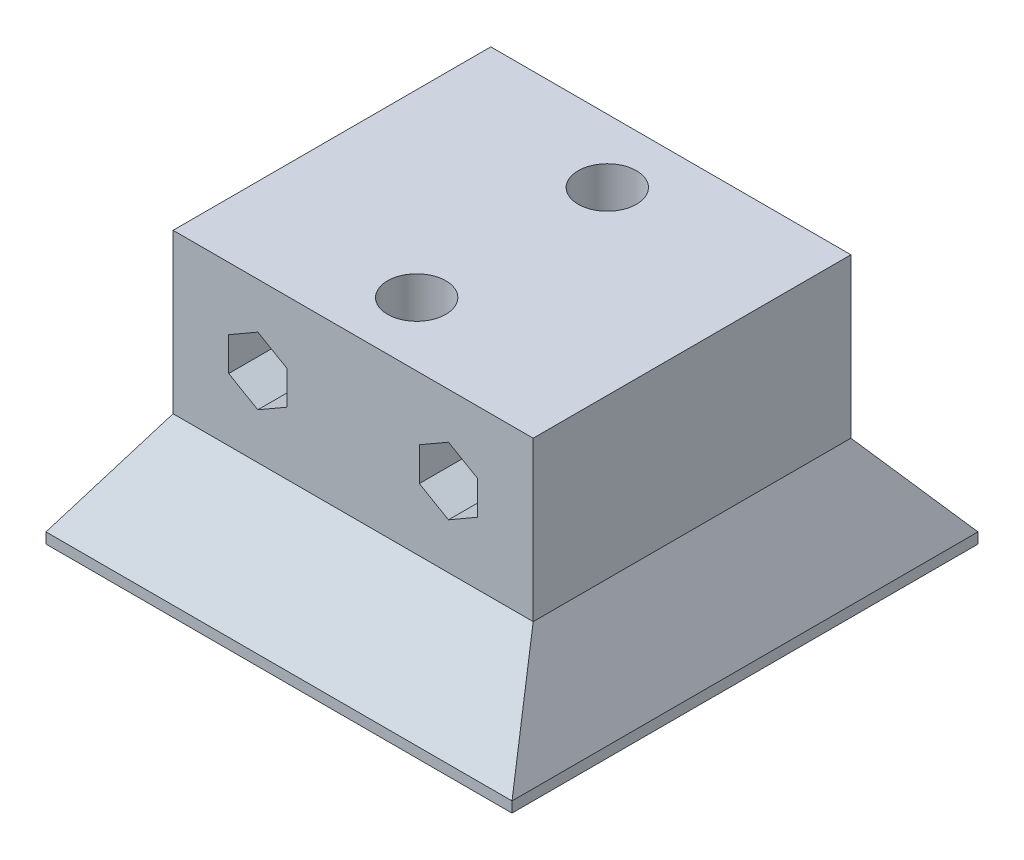
SolidWorks part; units mm, degrees
ref_plane "Front Plane" through (0, 0, 0) normal (0, 0, 1) x (1, 0, 0)
ref_plane "Top Plane" through (0, 0, 0) normal (0, 1, 0) x (1, 0, 0)
ref_plane "Right Plane" through (0, 0, 0) normal (1, 0, 0) x (0, 0, -1)
sketch "Sketch1" plane through (0, 0, 0) normal (0, 0, 1) x (1, 0, 0)
  line L1 (0, 0) -> (34, 0)
  line L2 (0, 0) -> (0, 15)
  line L3 (0, 15) -> (34, 15)
  line L4 (34, 0) -> (34, 15)
  dimension "D1" = 34
  dimension "D2" = 15
extrude "Boss-Extrude1" add sketch "Sketch1" along normal blind 30
sketch "Sketch3" plane through (0, 0, 30) normal (0, 0, 1) x (1, 0, 0)
  line L0 (0, 0) -> (-5, -8.6603)
  line L1 (-5, -9.6603) -> (39, -9.6603)
  line L2 (39, -8.6603) -> (34, 0)
  line L3 (0, 0) -> (34, 0) construction
  line L4 (0, 0) -> (34, 0)
  line L5 (-5, -8.6603) -> (-5, -9.6603)
  line L6 (39, -9.6603) -> (39, -8.6603)
  dimension "D1" = 120
  dimension "D2" = 120
  dimension "D3" = 44
  dimension "D4" = 1
extrude "Boss-Extrude2" add sketch "Sketch3" against normal blind 37 and the other way blind 7
sketch "Sketch5" plane through (0, 0, 30) normal (0, 0, 1) x (1, 0, 0)
  line L0 (34, 15) -> (0, 15) construction
  line L1 (8, 4.3246) -> (10.75, 5.9123)
  line L2 (10.75, 5.9123) -> (10.75, 9.0877)
  line L3 (10.75, 9.0877) -> (8, 10.6754)
  line L4 (8, 10.6754) -> (5.25, 9.0877)
  line L5 (5.25, 9.0877) -> (5.25, 5.9123)
  line L6 (5.25, 5.9123) -> (8, 4.3246)
  line L7 (26, 4.3246) -> (28.75, 5.9123)
  line L8 (28.75, 5.9123) -> (28.75, 9.0877)
  line L9 (28.75, 9.0877) -> (26, 10.6754)
  line L10 (26, 10.6754) -> (23.25, 9.0877)
  line L11 (23.25, 9.0877) -> (23.25, 5.9123)
  line L12 (23.25, 5.9123) -> (26, 4.3246)
  line L14 (0, 15) -> (0, 0) construction
  line L15 (34, 0) -> (34, 15) construction
  circle A0 centre (8, 7.5) radius 2.75 construction
  circle A1 centre (26, 7.5) radius 2.75 construction
  dimension "D1" = 7.5
  dimension "D2" = 7.5
  dimension "D3" = 8
  dimension "D4" = 5.5
  dimension "D5" = 5.5
  dimension "D6" = 8
extrude "Cut-Extrude2" cut sketch "Sketch5" against normal through all
sketch "Sketch6" plane through (0, 0, 0) normal (-1, 0, 0) x (0, 0, 1)
  line L0 (30, 0) -> (37, -8.6603)
  line L1 (37, -8.6603) -> (37, 0)
  line L2 (37, 0) -> (30, 0)
  line L3 (0, 0) -> (-7, -8.6603)
  line L4 (-7, -8.6603) -> (-7, 0)
  line L5 (-7, 0) -> (0, 0)
extrude "Cut-Extrude3" cut sketch "Sketch6" against normal through all and the other way through all
sketch "Sketch7" plane through (0, 15, 0) normal (0, 1, 0) x (1, 0, 0)
  line L0 (0, -30) -> (0, 0) construction
  line L1 (34, -30) -> (0, -30) construction
  line L2 (34, 0) -> (0, 0) construction
  circle A0 centre (17, -6) radius 2.75
  circle A1 centre (17, -24) radius 2.75
  point P8 (17, 0)
  dimension "D2" = 5.5
  dimension "D3" = 17
  dimension "D4" = 6
  dimension "D5" = 6
extrude "Cut-Extrude4" cut sketch "Sketch7" against normal through all
